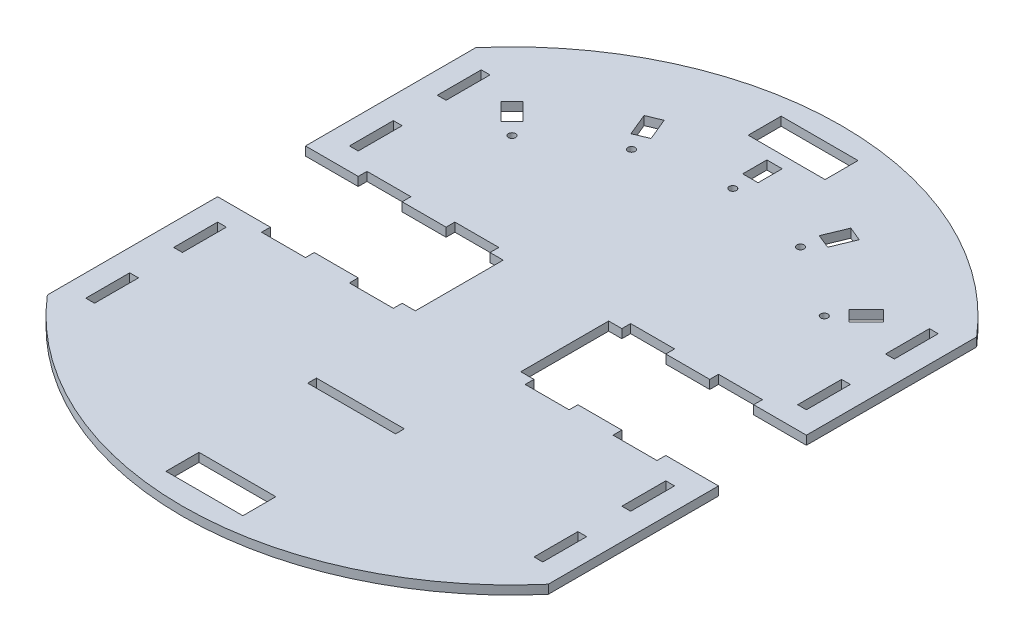
SolidWorks part; units mm, degrees
ref_plane "Přední rovina" through (0, 0, 0) normal (0, 0, 1) x (1, 0, 0)
ref_plane "Horní rovina" through (0, 0, 0) normal (0, 1, 0) x (1, 0, 0)
ref_plane "Pravá rovina" through (0, 0, 0) normal (1, 0, 0) x (0, 0, -1)
sketch "Skica1" plane through (0, 0, 0) normal (0, 1, 0) x (1, 0, 0)
  line L0 (-150, 0) -> (150, 0)
  line L9 (174, -97.4885) -> (114, -97.4885)
  line L10 (-174, 97.4885) -> (-114, 97.4885)
  line L17 (-100, -90) -> (-104, -90)
  line L18 (-100, -90) -> (-100, -70)
  line L19 (-100, -70) -> (-104, -70)
  line L20 (-104, -90) -> (-104, -70)
  line L21 (-100, -50) -> (-104, -50)
  line L22 (-100, -50) -> (-100, -30)
  line L23 (-100, -30) -> (-104, -30)
  line L24 (-104, -50) -> (-104, -30)
  line L25 (0, -150) -> (0, 150)
  line L26 (-100, 30) -> (-104, 30)
  line L27 (-104, 50) -> (-104, 30)
  line L28 (-100, 50) -> (-104, 50)
  line L29 (-100, 50) -> (-100, 30)
  line L30 (-100, 70) -> (-104, 70)
  line L31 (-104, 90) -> (-104, 70)
  line L32 (-100, 90) -> (-104, 90)
  line L33 (-100, 90) -> (-100, 70)
  line L36 (100, 90) -> (100, 70)
  line L37 (100, 90) -> (104, 90)
  line L38 (104, 90) -> (104, 70)
  line L39 (100, 70) -> (104, 70)
  line L40 (100, 50) -> (100, 30)
  line L41 (100, 50) -> (104, 50)
  line L42 (104, 50) -> (104, 30)
  line L43 (100, 30) -> (104, 30)
  line L44 (100, -30) -> (104, -30)
  line L45 (104, -50) -> (104, -30)
  line L46 (100, -50) -> (104, -50)
  line L47 (100, -50) -> (100, -30)
  line L48 (100, -70) -> (104, -70)
  line L49 (104, -90) -> (104, -70)
  line L50 (100, -90) -> (104, -90)
  line L51 (100, -90) -> (100, -70)
  line L80 (-64.4107, 0) -> (66.7662, 0) construction
  line L81 (24, 20) -> (114, 20)
  line L82 (90, 20) -> (90, 24)
  line L83 (-24, -20) -> (-114, -20)
  line L84 (90, 20) -> (70, 20)
  line L85 (50, -24) -> (30, -24)
  line L86 (-90, -20) -> (-70, -20)
  line L87 (-90, -20) -> (-90, -24)
  line L88 (-90, -24) -> (-70, -24)
  line L89 (-70, -20) -> (-70, -24)
  line L90 (-50, -20) -> (-30, -20)
  line L91 (-50, -20) -> (-50, -24)
  line L92 (-50, -24) -> (-30, -24)
  line L93 (-30, -20) -> (-30, -24)
  line L94 (-10, -20) -> (10, -20)
  line L95 (-10, -20) -> (-10, -24)
  line L96 (-10, -24) -> (10, -24)
  line L97 (10, -20) -> (10, -24)
  line L98 (30, -20) -> (30, -24)
  line L99 (50, -20) -> (30, -20)
  line L100 (50, -20) -> (50, -24)
  line L101 (90, -24) -> (70, -24)
  line L102 (70, -20) -> (70, -24)
  line L103 (90, -20) -> (70, -20)
  line L104 (90, -20) -> (90, -24)
  line L118 (-17.5, -140) -> (17.5, -140)
  line L119 (-17.5, -140) -> (-17.5, -125)
  line L120 (-17.5, -125) -> (17.5, -125)
  line L121 (17.5, -140) -> (17.5, -125)
  line L122 (-17.5, -140) -> (17.5, -125) construction
  line L123 (-17.5, -125) -> (17.5, -140) construction
  line L124 (-17.5, 125) -> (17.5, 125)
  line L125 (17.5, 140) -> (17.5, 125)
  line L126 (-17.5, 140) -> (17.5, 140)
  line L127 (-17.5, 140) -> (-17.5, 125)
  line L128 (-174, 97.4885) -> (-174, -97.4885)
  line L129 (-174, -97.4885) -> (-114, -97.4885)
  line L130 (-114, 97.4885) -> (-114, -97.4885)
  line L131 (-174, 97.4885) -> (-114, -97.4885) construction
  line L132 (-174, -97.4885) -> (-114, 97.4885) construction
  line L133 (114, 97.4885) -> (114, -97.4885)
  line L134 (174, 97.4885) -> (114, 97.4885)
  line L135 (174, 97.4885) -> (174, -97.4885)
  line L136 (-24, -20) -> (-24, 20)
  line L137 (-24, 20) -> (-114, 20)
  line L138 (-114, -20) -> (-114, 20)
  line L139 (114, -20) -> (114, 20)
  line L140 (24, -20) -> (114, -20)
  line L141 (24, -20) -> (24, 20)
  line L142 (70, 20) -> (70, 24)
  line L143 (90, 24) -> (70, 24)
  line L144 (50, 20) -> (50, 24)
  line L145 (50, 20) -> (30, 20)
  line L146 (30, 20) -> (30, 24)
  line L147 (50, 24) -> (30, 24)
  line L148 (-30, 20) -> (-30, 24)
  line L149 (-50, 24) -> (-30, 24)
  line L150 (-50, 20) -> (-50, 24)
  line L151 (-50, 20) -> (-30, 20)
  line L152 (-70, 20) -> (-70, 24)
  line L153 (-90, 24) -> (-70, 24)
  line L154 (-90, 20) -> (-90, 24)
  line L155 (-90, 20) -> (-70, 20)
  line L156 (48.9642, 109.0642) -> (44.7547, 98.9015)
  line L157 (-20, -69) -> (20, -69)
  line L158 (-20, -69) -> (-20, -73)
  line L159 (-20, -73) -> (20, -73)
  line L160 (20, -69) -> (20, -73)
  line L161 (-20, -69) -> (20, -73) construction
  line L162 (-20, -73) -> (20, -69) construction
  line L163 (-3.5, 119.5) -> (3.5, 119.5)
  line L164 (-3.5, 119.5) -> (-3.5, 108.5)
  line L165 (-3.5, 108.5) -> (3.5, 108.5)
  line L166 (3.5, 119.5) -> (3.5, 108.5)
  line L167 (-3.5, 119.5) -> (3.5, 108.5) construction
  line L168 (-3.5, 108.5) -> (3.5, 119.5) construction
  line L169 (38.2876, 101.5803) -> (44.7547, 98.9015)
  line L170 (42.4971, 111.743) -> (38.2876, 101.5803)
  line L171 (42.4971, 111.743) -> (48.9642, 109.0642)
  line L172 (86.9741, 82.0244) -> (79.196, 74.2462)
  line L173 (74.2462, 79.196) -> (79.196, 74.2462)
  line L174 (82.0244, 86.9741) -> (74.2462, 79.196)
  line L175 (82.0244, 86.9741) -> (86.9741, 82.0244)
  line L176 (-42.4971, 111.743) -> (-38.2876, 101.5803)
  line L177 (-44.7547, 98.9015) -> (-38.2876, 101.5803)
  line L178 (-48.9642, 109.0642) -> (-44.7547, 98.9015)
  line L179 (-48.9642, 109.0642) -> (-42.4971, 111.743)
  line L180 (-82.0244, 86.9741) -> (-74.2462, 79.196)
  line L181 (-79.196, 74.2462) -> (-74.2462, 79.196)
  line L182 (-86.9741, 82.0244) -> (-79.196, 74.2462)
  line L183 (-86.9741, 82.0244) -> (-82.0244, 86.9741)
  circle A0 centre (0, 0) radius 150
  arc A1 (-114, 0) -> (114, 0) centre (0, 0) cw construction
  circle A2 centre (0, 100.5) radius 1.625
  circle A3 centre (38.4597, 92.8499) radius 1.625
  circle A4 centre (71.0642, 71.0642) radius 1.625
  circle A5 centre (-38.4597, 92.8499) radius 1.625
  circle A6 centre (-71.0642, 71.0642) radius 1.625
  point P2 (-150, 0)
  point P4 (-144, 0)
  point P8 (150, 0)
  point P17 (-102, -90)
  point P72 (0, -71)
  point P79 (0, 114)
  point P101 (0, 0)
  point P127 (0, -132.5)
  point P147 (0, 0)
  dimension "D1" = 300
  dimension "D26" = 3
  dimension "D31" = 10
  dimension "D35" = 4
  dimension "D36" = 4
  dimension "D39" = 4
  dimension "D15" = 7
  dimension "D17" = 3.25
  dimension "D4" = 20
  dimension "D5" = 20
  dimension "D7" = 20
  dimension "D8" = 30
  dimension "D9" = 4
  dimension "D10" = 20
  dimension "D11" = 40
  dimension "D12" = 4
  dimension "D13" = 45
  dimension "D14" = 20
  dimension "D16" = 11
  dimension "D18" = 8
  dimension "D19" = 3
  dimension "D20" = 20
  dimension "D21" = 4
  dimension "D22" = 40
  dimension "D23" = 90
  dimension "D24" = 50
  dimension "D25" = 90
  dimension "D34" = 100
  dimension "D43" = 20
  dimension "D44" = 24
  dimension "D53" = 20
  dimension "D54" = 20
  dimension "D55" = 20
  dimension "D57" = 20
  dimension "D58" = 20
  dimension "D60" = 35
  dimension "D61" = 15
  dimension "D62" = 140
  dimension "D64" = 60
extrude "Přidat vysunutím1" add sketch "Skica1" along normal blind 4 contours L130 A0 L25 L118 L119 L120 L96 L95 L94 L0 L136 L83 L93 L92 L91 L89 L88 L87 L21 L24 L23 L22 L17 L20 L19 L18 | L95 L96 L25 L94 | L97 L94 L25 L96 | L25 A0 L133 L140 L104 L101 L102 L100 L85 L98 L141 L0 L94 L97 L96 L120 L121 L118 L50 L51 L48 L49 L46 L47 L44 L45 | L133 A0 L25 L126 L125 L124 L0 L141 L81 L39 L36 L37 L38 L43 L40 L41 L42 | L25 A0 L130 L137 L136 L0 L124 L127 L126 L32 L33 L30 L31 L28 L29 L26 L27 | L9
